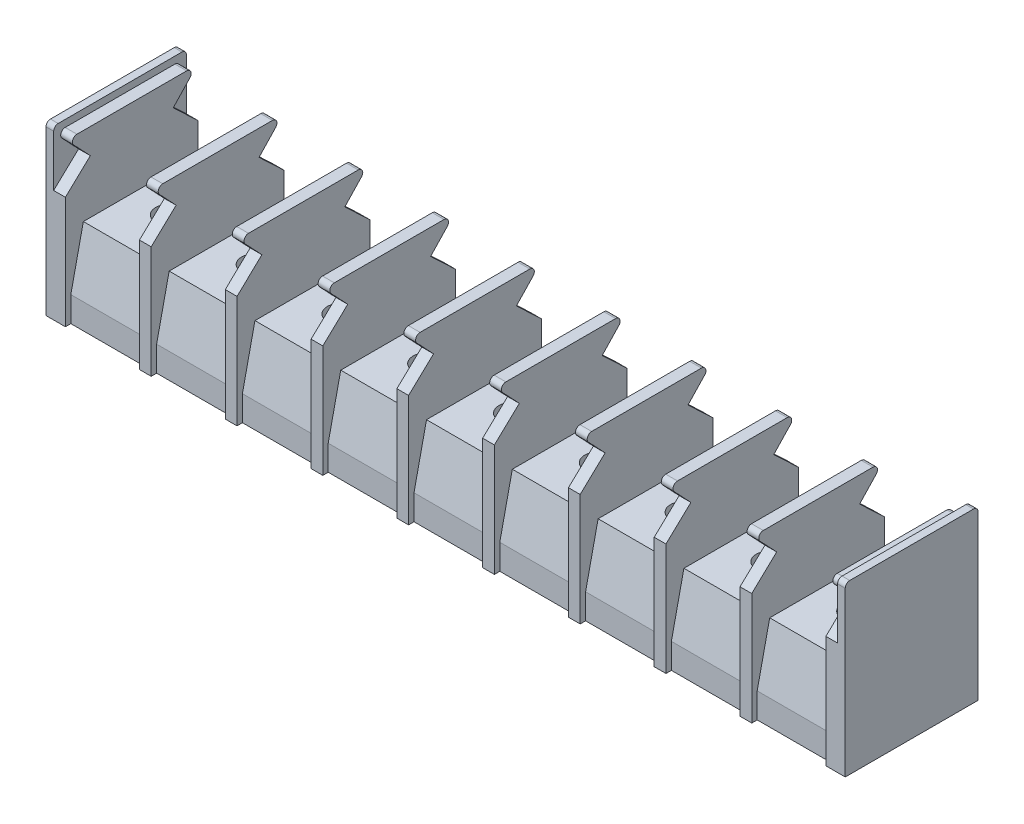
SolidWorks part; units mm, degrees
material "6061 Alloy"
ref_plane "Front Plane" through (0, 0, 0) normal (0, 0, 1) x (1, 0, 0)
ref_plane "Top Plane" through (0, 0, 0) normal (0, 1, 0) x (1, 0, 0)
ref_plane "Right Plane" through (0, 0, 0) normal (1, 0, 0) x (0, 0, -1)
sketch "Sketch1" plane through (0, 0, 0) normal (1, 0, 0) x (0, 0, -1)
  line L0 (6.75, 0) -> (7.35, 0) construction
  line L1 (-7.35, 0) -> (-6.75, 0) construction
  line L2 (-7.35, 0) -> (-7.35, 18.6) construction
  line L3 (-7.35, 18.6) -> (7.35, 18.6) construction
  line L4 (7.35, 0) -> (7.35, 18.6) construction
  line L5 (6.75, 0) -> (6.75, 2.79)
  line L6 (-6.75, 0) -> (-6.75, 2.79)
  line L7 (-6.75, 2.79) -> (-5.365, 9.1)
  line L8 (-5.365, 9.1) -> (5.365, 9.1)
  line L9 (5.365, 9.1) -> (6.75, 2.79)
  line L10 (-6.75, 0) -> (6.75, 0)
  line L11 (-6.75, 2.79) -> (6.75, 2.79) construction
  dimension "D1" = 18.6
  dimension "D2" = 14.7
  dimension "D3" = 1.2
  dimension "D4" = 10.73
  dimension "D5" = 9.1
  dimension "D6" = 2.79
extrude "Boss-Extrude1" add sketch "Sketch1" along normal mid plane 88.5
sketch "Sketch3" plane through (44.25, 0, 0) normal (1, 0, 0) x (0, 0, -1)
  line L0 (-6.75, 0) -> (-7.35, 0)
  line L1 (6.75, 0) -> (7.35, 0)
  line L2 (7.35, 0) -> (7.35, 18.1)
  line L3 (6.85, 18.6) -> (-6.85, 18.6)
  line L4 (-7.35, 18.1) -> (-7.35, 0)
  line L6 (-6.75, 0) -> (6.75, 0)
  line L7 (6.75, 0) -> (6.75, 2.79)
  line L8 (6.75, 2.79) -> (5.365, 9.1)
  line L9 (5.365, 9.1) -> (-5.365, 9.1)
  line L10 (-5.365, 9.1) -> (-6.75, 2.79)
  line L11 (-6.75, 2.79) -> (-6.75, 0)
  line L13 (6.75, 0) -> (6.75, 2.79)
  line L14 (6.75, 2.79) -> (5.365, 9.1)
  line L15 (5.365, 9.1) -> (-5.365, 9.1)
  line L16 (-5.365, 9.1) -> (-6.75, 2.79)
  line L17 (-6.75, 2.79) -> (-6.75, 0)
  arc A0 (6.85, 18.6) -> (7.35, 18.1) centre (6.85, 18.1) cw
  arc A1 (-6.85, 18.6) -> (-7.35, 18.1) centre (-6.85, 18.1) ccw
  point P13 (7.35, 18.6)
  point P16 (-7.35, 18.6)
  dimension "D4" = 0.5
  dimension "D2" = 18.6
  dimension "D3" = 14.7
  dimension "D1" = 0
extrude "Boss-Extrude2" add sketch "Sketch3" against normal blind 0.85
mirror "Mirror1" about plane through (0, 0, 0) normal (1, 0, 0) of "Boss-Extrude2"
sketch "Sketch4" plane through (43.4, 0, 0) normal (-1, 0, 0) x (0, 0, 1)
  line L0 (-7.35, 0) -> (-7.35, 18.1) construction
  line L1 (7.35, 18.1) -> (7.35, 0) construction
  line L2 (-6.75, 2.79) -> (-6.75, 0) construction
  line L3 (7.35, 12.42) -> (7.35, 0)
  line L4 (7.35, 0) -> (6.75, 0) construction
  line L5 (-5.365, 9.1) -> (-6.75, 2.79) construction
  line L6 (-7.35, 12.42) -> (-4.5889, 15.03)
  line L7 (7.35, 12.42) -> (4.5889, 15.03)
  line L8 (4.5889, 15.03) -> (6.4384, 16.9865)
  line L9 (-4.5889, 15.03) -> (-6.4384, 16.9865)
  line L10 (-6.75, 0) -> (-7.35, 0) construction
  line L11 (-7.35, 12.42) -> (7.35, 12.42) construction
  line L12 (-6.075, 17.83) -> (6.075, 17.83)
  line L13 (-7.35, 0) -> (-7.35, 12.42)
  line L14 (-6.75, 0) -> (-7.35, 0)
  line L15 (7.35, 0) -> (6.75, 0)
  line L16 (5.365, 9.1) -> (-5.365, 9.1) construction
  line L17 (-6.85, 18.6) -> (6.85, 18.6) construction
  line L18 (-6.75, 2.79) -> (-6.75, 0)
  line L19 (-5.365, 9.1) -> (-6.75, 2.79)
  line L20 (5.365, 9.1) -> (-5.365, 9.1)
  line L21 (6.75, 0) -> (6.75, 2.79) construction
  line L22 (6.75, 2.79) -> (5.365, 9.1) construction
  line L23 (6.75, 0) -> (6.75, 2.79)
  line L24 (6.75, 2.79) -> (5.365, 9.1)
  line L25 (-6.575, 12.42) -> (-6.575, 18.6) construction
  line L26 (-6.85, 18.6) -> (6.85, 18.6) construction
  line L27 (6.575, 12.42) -> (6.575, 18.6) construction
  arc A3 (6.075, 17.83) -> (6.4384, 16.9865) centre (6.075, 17.33) cw
  arc A4 (-6.075, 17.83) -> (-6.4384, 16.9865) centre (-6.075, 17.33) ccw
  arc A5 (-6.075, 17.83) -> (-6.4384, 16.9865) centre (-6.075, 17.33) ccw
  line M1 (6.75, 2.79) -> (6.75, 0)
  line M2 (6.75, 0) -> (7.35, 0)
  line M3 (7.35, 0) -> (7.35, 18.1)
  line M7 (-7.35, 18.1) -> (-7.35, 0)
  line M8 (-7.35, 0) -> (-6.75, 0)
  line M9 (-6.75, 0) -> (-6.75, 2.79)
  line M10 (-6.75, 2.79) -> (-5.365, 9.1)
  line M11 (-5.365, 9.1) -> (5.365, 9.1)
  line M12 (5.365, 9.1) -> (6.75, 2.79)
  dimension "D3" = 0.5
  dimension "D1" = 12.42
  dimension "D2" = 0.77
  dimension "D4" = 2.8
  dimension "D5" = 13.15
extrude "Boss-Extrude3" add sketch "Sketch4" along normal blind 1.3 contours L12 A4 L9 L6 L7 L8 A3 M7 M8 M9 M10 M11 M12 M1 M2 M3
pattern_linear "LPattern1" count 10 spacing 9.5 along (-1, 0, 0) of "Boss-Extrude3"
hole_wizard "M3.5x0.6 Tapped Hole1" positions "Sketch6" profile "Sketch5" tap size "M3.5x0.6" standard "ANSI Metric"
sketch "Sketch6" plane through (0, 9.1, 0) normal (0, 1, 0) x (1, 0, 0)
  line L6 (-42.1, 0) -> (-33.9, 0) construction
  line L8 (-33.9, 5.365) -> (-33.9, -5.365) construction
  line L9 (-32.6, 0) -> (-24.4, 0) construction
  line L11 (-24.4, 5.365) -> (-24.4, -5.365) construction
  line L12 (-23.1, 0) -> (-14.9, 0) construction
  line L14 (-14.9, 5.365) -> (-14.9, -5.365) construction
  line L15 (-13.6, 0) -> (-5.4, 0) construction
  line L17 (-5.4, 5.365) -> (-5.4, -5.365) construction
  line L21 (5.4, 0) -> (13.6, 0) construction
  line L22 (5.4, 5.365) -> (5.4, -5.365) construction
  line L24 (14.9, 0) -> (23.1, 0) construction
  line L26 (23.1, 5.365) -> (23.1, -5.365) construction
  line L27 (24.4, 0) -> (32.6, 0) construction
  line L28 (24.4, 5.365) -> (24.4, -5.365) construction
  line L30 (33.9, 0) -> (42.1, 0) construction
  line L32 (42.1, 5.365) -> (42.1, -5.365) construction
  line L33 (-42.1, 5.365) -> (-42.1, -5.365) construction
  line L34 (-32.6, 5.365) -> (-32.6, -5.365) construction
  line L35 (-23.1, 5.365) -> (-23.1, -5.365) construction
  line L36 (-13.6, 5.365) -> (-13.6, -5.365) construction
  line L37 (13.6, 5.365) -> (13.6, -5.365) construction
  line L38 (14.9, 5.365) -> (14.9, -5.365) construction
  line L39 (32.6, 5.365) -> (32.6, -5.365) construction
  line L40 (33.9, 5.365) -> (33.9, -5.365) construction
  point P0 (-38, 0)
  point P2 (-28.5, 0)
  point P4 (-19, 0)
  point P6 (-9.5, 0)
  point P8 (0, 0)
  point P11 (9.5, 0)
  point P13 (19, 0)
  point P15 (28.5, 0)
  point P17 (38, 0)
sketch "Sketch5" plane through (-38, 9.1, 0) normal (1, 0, 0) x (0, 0, 1)
  line L0 (0, 0) -> (0, 8.8712)
  line L1 (0, 8.8712) -> (1.45, 8)
  line L2 (1.45, 8) -> (1.45, 0)
  line L5 (1.45, 0) -> (0, 0)
  line L10 (0, 8.8712) -> (-1.45, 8) construction
  line L11 (0, -6.35) -> (0, 107.95) construction
  dimension "Tap Drill Dia." = 2.9
  dimension "Tap Drill Depth" = 8
  dimension "Drill Angle" = 118
cosmetic thread "Hole Thread1" parameters "D1"=6, "D2"=3.5
cosmetic thread "Hole Thread2" parameters "D1"=6, "D2"=3.5
cosmetic thread "Hole Thread3" parameters "D1"=6, "D2"=3.5
cosmetic thread "Hole Thread4" parameters "D1"=6, "D2"=3.5
cosmetic thread "Hole Thread5" parameters "D1"=6, "D2"=3.5
cosmetic thread "Hole Thread6" parameters "D1"=6, "D2"=3.5
cosmetic thread "Hole Thread7" parameters "D1"=6, "D2"=3.5
cosmetic thread "Hole Thread8" parameters "D1"=6, "D2"=3.5
cosmetic thread "Hole Thread9" parameters "D1"=6, "D2"=3.5
